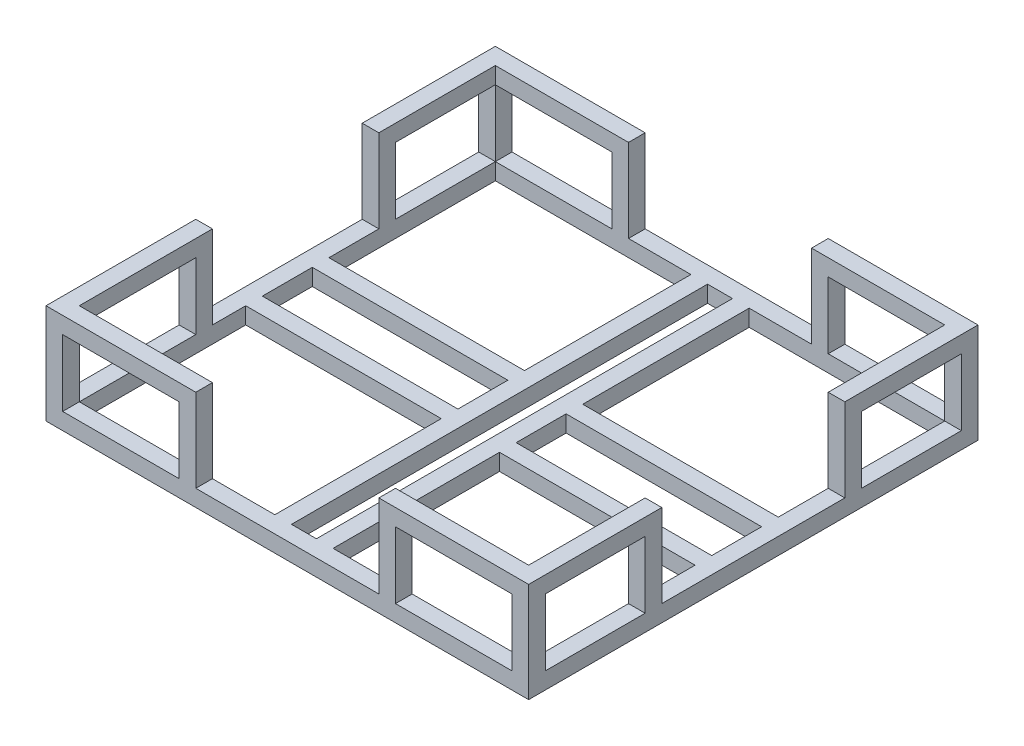
SolidWorks part; units mm, degrees
ref_plane "前视基准面" through (0, 0, 0) normal (0, 0, 1) x (1, 0, 0)
ref_plane "上视基准面" through (0, 0, 0) normal (0, 1, 0) x (1, 0, 0)
ref_plane "右视基准面" through (0, 0, 0) normal (1, 0, 0) x (0, 0, -1)
sketch "草图2" plane through (0, 0, 0) normal (0, 1, 0) x (1, 0, 0)
  line L1 (-272.9412, 158.0784) -> (307.0588, 158.0784)
  line L2 (-272.9412, 158.0784) -> (-272.9412, -381.9216)
  line L3 (-272.9412, -381.9216) -> (307.0588, -381.9216)
  line L4 (307.0588, 158.0784) -> (307.0588, -381.9216)
  dimension "D1" = 580
extrude "凸台-拉伸1" add sketch "草图2" along normal blind 20
sketch "草图3" plane through (0, 20, 0) normal (0, 1, 0) x (1, 0, 0)
  line L0 (-272.9412, 158.0784) -> (-252.9412, 158.0784) construction
  line L1 (307.0588, 158.0784) -> (-272.9412, 158.0784) construction
  line L2 (-252.9412, 158.0784) -> (-252.9412, 138.0784) construction
  line L4 (-252.9412, 138.0784) -> (-17.9412, 138.0784)
  line L5 (-252.9412, 138.0784) -> (-252.9412, -61.9216)
  line L6 (-252.9412, -61.9216) -> (-17.9412, -61.9216)
  line L7 (-17.9412, 138.0784) -> (-17.9412, -61.9216)
  dimension "D1" = 235
  dimension "D2" = 200
extrude "切除-拉伸1" cut sketch "草图3" against normal through all contours L5 L4 L7 L6
sketch "草图4" plane through (0, 20, 0) normal (0, 1, 0) x (1, 0, 0)
  line L0 (307.0588, 158.0784) -> (287.0588, 158.0784) construction
  line L1 (307.0588, 158.0784) -> (-272.9412, 158.0784) construction
  line L2 (287.0588, 158.0784) -> (287.0588, 138.0784) construction
  line L4 (287.0588, 138.0784) -> (52.0588, 138.0784)
  line L5 (287.0588, 138.0784) -> (287.0588, -61.9216)
  line L6 (287.0588, -61.9216) -> (52.0588, -61.9216)
  line L7 (52.0588, 138.0784) -> (52.0588, -61.9216)
  point P9 (0, 0)
  dimension "D1" = 235
extrude "切除-拉伸2" cut sketch "草图4" against normal through all contours L5 L4 L7 L6
sketch "草图5" plane through (0, 20, 0) normal (0, 1, 0) x (1, 0, 0)
  line L0 (-272.9412, -381.9216) -> (-252.9412, -381.9216) construction
  line L1 (-272.9412, -381.9216) -> (307.0588, -381.9216) construction
  line L2 (-252.9412, -381.9216) -> (-252.9412, -361.9216) construction
  line L4 (-252.9412, -361.9216) -> (-17.9412, -361.9216)
  line L5 (-252.9412, -361.9216) -> (-252.9412, -161.9216)
  line L6 (-252.9412, -161.9216) -> (-17.9412, -161.9216)
  line L7 (-17.9412, -361.9216) -> (-17.9412, -161.9216)
  point P7 (-252.9412, -361.9216)
  dimension "D1" = 200
extrude "切除-拉伸3" cut sketch "草图5" against normal through all contours L5 L4 L7 L6
sketch "草图6" plane through (0, 20, 0) normal (0, 1, 0) x (1, 0, 0)
  line L0 (307.0588, -381.9216) -> (287.0588, -381.9216) construction
  line L1 (-272.9412, -381.9216) -> (307.0588, -381.9216) construction
  line L2 (287.0588, -381.9216) -> (287.0588, -361.9216) construction
  line L4 (287.0588, -361.9216) -> (52.0588, -361.9216)
  line L5 (287.0588, -361.9216) -> (287.0588, -161.9216)
  line L6 (287.0588, -161.9216) -> (52.0588, -161.9216)
  line L7 (52.0588, -361.9216) -> (52.0588, -161.9216)
  point P7 (287.0588, -361.9216)
extrude "切除-拉伸4" cut sketch "草图6" against normal through all
sketch "草图7" plane through (0, 20, 0) normal (0, 1, 0) x (1, 0, 0)
  line L0 (-17.9412, -361.9216) -> (2.0588, -361.9216) construction
  line L1 (-17.9412, -361.9216) -> (-17.9412, -161.9216) construction
  line L2 (-252.9412, -361.9216) -> (-17.9412, -361.9216) construction
  line L3 (52.0588, -361.9216) -> (32.0588, -361.9216) construction
  line L4 (52.0588, -161.9216) -> (52.0588, -361.9216) construction
  line L5 (-17.9412, 138.0784) -> (2.0588, 138.0784) construction
  line L6 (52.0588, 138.0784) -> (32.0588, 138.0784) construction
  line L7 (287.0588, 138.0784) -> (52.0588, 138.0784) construction
  line L8 (52.0588, 138.0784) -> (52.0588, -61.9216) construction
  line L10 (2.0588, 138.0784) -> (32.0588, 138.0784)
  line L11 (2.0588, 138.0784) -> (2.0588, -361.9216)
  line L12 (2.0588, -361.9216) -> (32.0588, -361.9216)
  line L13 (32.0588, 138.0784) -> (32.0588, -361.9216)
extrude "切除-拉伸5" cut sketch "草图7" against normal through all
sketch "草图8" plane through (0, 20, 0) normal (0, 1, 0) x (1, 0, 0)
  line L0 (-252.9412, -61.9216) -> (-252.9412, -81.9216) construction
  line L1 (-252.9412, -161.9216) -> (-252.9412, -141.9216) construction
  line L2 (-17.9412, -61.9216) -> (-17.9412, -81.9216) construction
  line L3 (-17.9412, -161.9216) -> (-17.9412, -141.9216) construction
  line L4 (-252.9412, -161.9216) -> (-17.9412, -161.9216) construction
  line L5 (52.0588, -61.9216) -> (52.0588, -81.9216) construction
  line L6 (287.0588, -61.9216) -> (52.0588, -61.9216) construction
  line L7 (52.0588, -161.9216) -> (52.0588, -141.9216) construction
  line L8 (287.0588, -61.9216) -> (287.0588, -81.9216) construction
  line L9 (287.0588, -161.9216) -> (287.0588, -141.9216) construction
  line L11 (-252.9412, -81.9216) -> (-17.9412, -81.9216)
  line L12 (-252.9412, -81.9216) -> (-252.9412, -141.9216)
  line L13 (-252.9412, -141.9216) -> (-17.9412, -141.9216)
  line L14 (-17.9412, -81.9216) -> (-17.9412, -141.9216)
extrude "切除-拉伸6" cut sketch "草图8" against normal through all
sketch "草图9" plane through (0, 20, 0) normal (0, 1, 0) x (1, 0, 0)
  line L0 (52.0588, -61.9216) -> (52.0588, -81.9216) construction
  line L1 (287.0588, -161.9216) -> (287.0588, -141.9216) construction
  line L2 (287.0588, -361.9216) -> (287.0588, -161.9216) construction
  line L3 (287.0588, -161.9216) -> (52.0588, -161.9216) construction
  line L5 (52.0588, -81.9216) -> (287.0588, -81.9216)
  line L6 (52.0588, -81.9216) -> (52.0588, -141.9216)
  line L7 (52.0588, -141.9216) -> (287.0588, -141.9216)
  line L8 (287.0588, -81.9216) -> (287.0588, -141.9216)
extrude "切除-拉伸7" cut sketch "草图9" against normal through all contours L6 L5 L8 L7
sketch "草图10" plane through (0, 20, 0) normal (0, 1, 0) x (1, 0, 0)
  line L0 (-252.9412, 138.0784) -> (-17.9412, 138.0784) construction
  line L1 (-272.9412, 158.0784) -> (-92.9412, 158.0784)
  line L2 (-272.9412, 158.0784) -> (-272.9412, 138.0784)
  line L3 (-272.9412, 138.0784) -> (-92.9412, 138.0784)
  line L4 (-92.9412, 158.0784) -> (-92.9412, 138.0784)
  dimension "D1" = 180
extrude "凸台-拉伸2" add sketch "草图10" along normal blind 100
sketch "草图11" plane through (0, 0, -138.0784) normal (0, 0, 1) x (1, 0, 0)
  line L0 (-252.9412, 20) -> (-252.9412, 40) construction
  line L1 (-92.9412, 20) -> (-112.9412, 20) construction
  line L2 (-112.9412, 20) -> (-112.9412, 40) construction
  line L3 (-272.9412, 120) -> (-252.9412, 120) construction
  line L4 (-272.9412, 120) -> (-92.9412, 120) construction
  line L5 (-252.9412, 120) -> (-252.9412, 100) construction
  line L7 (-252.9412, 100) -> (-112.9412, 100)
  line L8 (-252.9412, 100) -> (-252.9412, 20)
  line L9 (-252.9412, 20) -> (-112.9412, 20)
  line L10 (-112.9412, 100) -> (-112.9412, 20)
extrude "切除-拉伸8" cut sketch "草图11" against normal through all
sketch "草图12" plane through (0, 20, 0) normal (0, 1, 0) x (1, 0, 0)
  line L0 (-272.9412, 138.0784) -> (-252.9412, 138.0784) construction
  line L1 (-272.9412, 138.0784) -> (-252.9412, 138.0784)
  line L2 (-272.9412, 138.0784) -> (-272.9412, -1.9216)
  line L3 (-272.9412, -1.9216) -> (-252.9412, -1.9216)
  line L4 (-252.9412, 138.0784) -> (-252.9412, -1.9216)
  line L5 (-252.9412, 138.0784) -> (-252.9412, -61.9216) construction
  dimension "D1" = 140
extrude "凸台-拉伸3" add sketch "草图12" along normal blind 100
sketch "草图13" plane through (-252.9412, 0, 0) normal (1, 0, 0) x (0, 0, -1)
  line L0 (-1.9216, 120) -> (18.0784, 120) construction
  line L1 (-1.9216, 120) -> (138.0784, 120) construction
  line L2 (18.0784, 120) -> (18.0784, 100) construction
  line L4 (18.0784, 100) -> (138.0784, 100)
  line L5 (18.0784, 100) -> (18.0784, 20)
  line L6 (18.0784, 20) -> (138.0784, 20)
  line L7 (138.0784, 100) -> (138.0784, 20)
extrude "切除-拉伸9" cut sketch "草图13" against normal through all
sketch "草图14" plane through (0, 20, 0) normal (0, 1, 0) x (1, 0, 0)
  line L0 (-252.9412, -361.9216) -> (-17.9412, -361.9216) construction
  line L1 (-272.9412, -381.9216) -> (-92.9412, -381.9216)
  line L2 (-272.9412, -381.9216) -> (-272.9412, -361.9216)
  line L3 (-272.9412, -361.9216) -> (-92.9412, -361.9216)
  line L4 (-92.9412, -381.9216) -> (-92.9412, -361.9216)
  dimension "D1" = 180
extrude "凸台-拉伸4" add sketch "草图14" along normal blind 100
sketch "草图15" plane through (0, 0, 361.9216) normal (0, 0, -1) x (-1, 0, 0)
  line L0 (92.9412, 120) -> (112.9412, 120) construction
  line L1 (92.9412, 120) -> (272.9412, 120) construction
  line L2 (92.9412, 120) -> (92.9412, 20) construction
  line L3 (112.9412, 120) -> (112.9412, 100) construction
  line L5 (112.9412, 100) -> (252.9412, 100)
  line L6 (112.9412, 100) -> (112.9412, 20)
  line L7 (112.9412, 20) -> (252.9412, 20)
  line L8 (252.9412, 100) -> (252.9412, 20)
extrude "切除-拉伸10" cut sketch "草图15" against normal through all
sketch "草图17" plane through (0, 20, 0) normal (0, 1, 0) x (1, 0, 0)
  line L0 (-252.9412, -361.9216) -> (-252.9412, -161.9216) construction
  line L1 (-272.9412, -361.9216) -> (-252.9412, -361.9216)
  line L2 (-272.9412, -361.9216) -> (-272.9412, -201.9216)
  line L3 (-272.9412, -201.9216) -> (-252.9412, -201.9216)
  line L4 (-252.9412, -361.9216) -> (-252.9412, -201.9216)
  dimension "D1" = 160
extrude "凸台-拉伸5" add sketch "草图17" along normal blind 100 contours L2 L1 L4 L3
sketch "草图18" plane through (-252.9412, 0, 0) normal (1, 0, 0) x (0, 0, -1)
  line L0 (-201.9216, 20) -> (-221.9216, 20) construction
  line L2 (-361.9216, 100) -> (-221.9216, 100)
  line L3 (-361.9216, 100) -> (-361.9216, 20)
  line L4 (-361.9216, 20) -> (-221.9216, 20)
  line L5 (-221.9216, 100) -> (-221.9216, 20)
extrude "切除-拉伸11" cut sketch "草图18" against normal through all
sketch "草图19" plane through (0, 20, 0) normal (0, 1, 0) x (1, 0, 0)
  line L0 (287.0588, 138.0784) -> (52.0588, 138.0784) construction
  line L1 (307.0588, 158.0784) -> (127.0588, 158.0784)
  line L2 (307.0588, 158.0784) -> (307.0588, 138.0784)
  line L3 (307.0588, 138.0784) -> (127.0588, 138.0784)
  line L4 (127.0588, 158.0784) -> (127.0588, 138.0784)
  dimension "D1" = 180
extrude "凸台-拉伸6" add sketch "草图19" along normal blind 100
sketch "草图20" plane through (0, 0, -138.0784) normal (0, 0, 1) x (1, 0, 0)
  line L0 (127.0588, 120) -> (147.0588, 120) construction
  line L1 (127.0588, 120) -> (307.0588, 120) construction
  line L2 (147.0588, 120) -> (147.0588, 100) construction
  line L4 (147.0588, 100) -> (287.0588, 100)
  line L5 (147.0588, 100) -> (147.0588, 20)
  line L6 (147.0588, 20) -> (287.0588, 20)
  line L7 (287.0588, 100) -> (287.0588, 20)
extrude "切除-拉伸12" cut sketch "草图20" against normal through all
sketch "草图22" plane through (0, 20, 0) normal (0, 1, 0) x (1, 0, 0)
  line L0 (307.0588, -381.9216) -> (307.0588, 138.0784) construction
  line L1 (287.0588, 138.0784) -> (307.0588, 138.0784)
  line L2 (287.0588, 138.0784) -> (287.0588, -1.9216)
  line L3 (287.0588, -1.9216) -> (307.0588, -1.9216)
  line L4 (307.0588, 138.0784) -> (307.0588, -1.9216)
  dimension "D1" = 140
extrude "凸台-拉伸7" add sketch "草图22" along normal blind 100
sketch "草图23" plane through (307.0588, 0, 0) normal (1, 0, 0) x (0, 0, -1)
  line L0 (-1.9216, 120) -> (18.0784, 120) construction
  line L1 (18.0784, 120) -> (18.0784, 100) construction
  line L2 (158.0784, 0) -> (158.0784, 20) construction
  line L3 (158.0784, 120) -> (158.0784, 0) construction
  line L4 (158.0784, 20) -> (138.0784, 20) construction
  line L6 (18.0784, 100) -> (138.0784, 100)
  line L7 (18.0784, 100) -> (18.0784, 20)
  line L8 (18.0784, 20) -> (138.0784, 20)
  line L9 (138.0784, 100) -> (138.0784, 20)
extrude "切除-拉伸13" cut sketch "草图23" against normal through all
sketch "草图24" plane through (0, 20, 0) normal (0, 1, 0) x (1, 0, 0)
  line L0 (52.0588, -361.9216) -> (287.0588, -361.9216) construction
  line L1 (307.0588, -381.9216) -> (127.0588, -381.9216)
  line L2 (307.0588, -381.9216) -> (307.0588, -361.9216)
  line L3 (307.0588, -361.9216) -> (127.0588, -361.9216)
  line L4 (127.0588, -381.9216) -> (127.0588, -361.9216)
  dimension "D1" = 180
extrude "凸台-拉伸8" add sketch "草图24" along normal blind 100
sketch "草图25" plane through (0, 0, 361.9216) normal (0, 0, -1) x (-1, 0, 0)
  line L0 (-307.0588, 120) -> (-287.0588, 120) construction
  line L1 (-307.0588, 120) -> (-127.0588, 120) construction
  line L2 (-127.0588, 20) -> (-147.0588, 20) construction
  line L3 (-127.0588, 120) -> (-147.0588, 120) construction
  line L4 (-127.0588, 120) -> (-127.0588, 20) construction
  line L5 (-147.0588, 120) -> (-147.0588, 100) construction
  line L7 (-147.0588, 100) -> (-287.0588, 100)
  line L8 (-147.0588, 100) -> (-147.0588, 20)
  line L9 (-147.0588, 20) -> (-287.0588, 20)
  line L10 (-287.0588, 100) -> (-287.0588, 20)
extrude "切除-拉伸14" cut sketch "草图25" against normal blind 100
sketch "草图26" plane through (0, 20, 0) normal (0, 1, 0) x (1, 0, 0)
  line L0 (287.0588, -361.9216) -> (287.0588, -161.9216) construction
  line L1 (307.0588, -361.9216) -> (287.0588, -361.9216)
  line L2 (307.0588, -361.9216) -> (307.0588, -221.9216)
  line L3 (307.0588, -221.9216) -> (287.0588, -221.9216)
  line L4 (287.0588, -361.9216) -> (287.0588, -221.9216)
  dimension "D1" = 140
extrude "凸台-拉伸9" add sketch "草图26" along normal blind 100
sketch "草图27" plane through (287.0588, 0, 0) normal (-1, 0, 0) x (0, 0, 1)
  line L0 (221.9216, 120) -> (241.9216, 120) construction
  line L1 (221.9216, 120) -> (361.9216, 120) construction
  line L2 (241.9216, 120) -> (241.9216, 100) construction
  line L4 (241.9216, 100) -> (361.9216, 100)
  line L5 (241.9216, 100) -> (241.9216, 20)
  line L6 (241.9216, 20) -> (361.9216, 20)
  line L7 (361.9216, 100) -> (361.9216, 20)
extrude "切除-拉伸15" cut sketch "草图27" against normal blind 100
